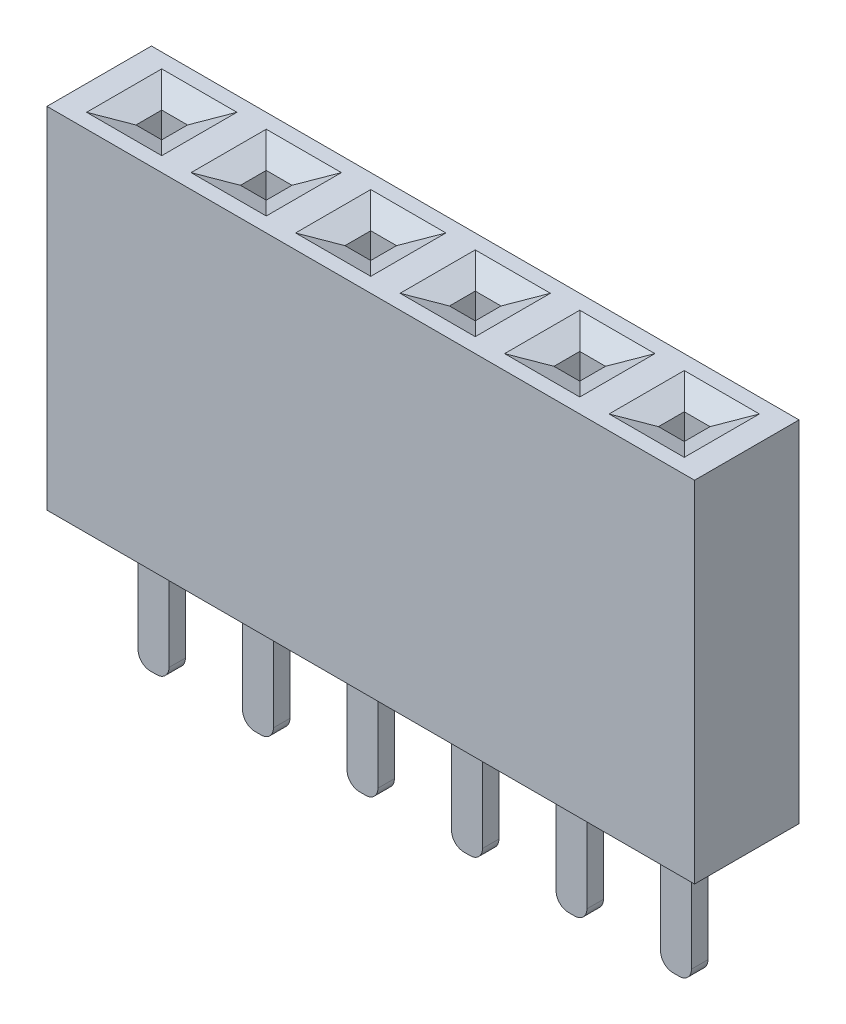
SolidWorks part; units mm, degrees
ref_plane "Plan de face" through (0, 0, 0) normal (0, 0, 1) x (1, 0, 0)
ref_plane "Plan de dessus" through (0, 0, 0) normal (0, 1, 0) x (1, 0, 0)
ref_plane "Plan de droite" through (0, 0, 0) normal (1, 0, 0) x (0, 0, -1)
sketch "Esquisse1" plane through (0, 0, 0) normal (0, 1, 0) x (1, 0, 0)
  line L1 (-7.87, 1.27) -> (7.87, 1.27)
  line L2 (-7.87, 1.27) -> (-7.87, -1.27)
  line L3 (-7.87, -1.27) -> (7.87, -1.27)
  line L4 (7.87, 1.27) -> (7.87, -1.27)
  line L5 (-7.87, 1.27) -> (7.87, -1.27) construction
  line L6 (-7.87, -1.27) -> (7.87, 1.27) construction
  point P0 (0, 0)
  dimension "D1" = 15.74
  dimension "D2" = 2.54
extrude "Boss.-Extru.1" add sketch "Esquisse1" along normal blind 8.5
sketch "Esquisse3" plane through (0, 8.5, 0) normal (0, 1, 0) x (1, 0, 0)
  line L0 (-8.36, 0.82) -> (8.2693, 0.82) construction
  line L1 (-8.36, -0.82) -> (8.2693, -0.82) construction
  line L2 (7.87, 1.27) -> (-7.87, 1.27) construction
  line L3 (-7.87, -1.27) -> (7.87, -1.27) construction
  line L4 (1.27, 1.6017) -> (1.27, -1.7521) construction
  line L5 (3.81, 1.6017) -> (3.81, -1.7521) construction
  line L6 (6.35, 1.6017) -> (6.35, -1.7521) construction
  line L7 (-1.27, 1.6017) -> (-1.27, -1.7521) construction
  line L8 (-3.81, 1.6017) -> (-3.81, -1.7521) construction
  line L9 (-6.35, 1.6017) -> (-6.35, -1.8488) construction
  line L10 (-8.36, 0) -> (8.2693, 0) construction
  line L12 (-2.09, 0.82) -> (-0.45, 0.82)
  line L13 (-2.09, 0.82) -> (-2.09, -0.82)
  line L14 (-2.09, -0.82) -> (-0.45, -0.82)
  line L15 (-0.45, 0.82) -> (-0.45, -0.82)
  line L16 (-2.09, 0.82) -> (-0.45, -0.82) construction
  line L17 (-2.09, -0.82) -> (-0.45, 0.82) construction
  line L18 (-4.63, 0.82) -> (-2.99, 0.82)
  line L19 (-4.63, 0.82) -> (-4.63, -0.82)
  line L20 (-4.63, -0.82) -> (-2.99, -0.82)
  line L21 (-2.99, 0.82) -> (-2.99, -0.82)
  line L22 (-4.63, 0.82) -> (-2.99, -0.82) construction
  line L23 (-4.63, -0.82) -> (-2.99, 0.82) construction
  line L24 (-7.17, 0.82) -> (-5.53, 0.82)
  line L25 (-7.17, 0.82) -> (-7.17, -0.82)
  line L26 (-7.17, -0.82) -> (-5.53, -0.82)
  line L27 (-5.53, 0.82) -> (-5.53, -0.82)
  line L28 (-7.17, 0.82) -> (-5.53, -0.82) construction
  line L29 (-7.17, -0.82) -> (-5.53, 0.82) construction
  line L30 (0.45, 0.82) -> (2.09, 0.82)
  line L31 (0.45, 0.82) -> (0.45, -0.82)
  line L32 (0.45, -0.82) -> (2.09, -0.82)
  line L33 (2.09, 0.82) -> (2.09, -0.82)
  line L34 (0.45, 0.82) -> (2.09, -0.82) construction
  line L35 (0.45, -0.82) -> (2.09, 0.82) construction
  line L36 (2.99, 0.82) -> (4.63, 0.82)
  line L37 (2.99, 0.82) -> (2.99, -0.82)
  line L38 (2.99, -0.82) -> (4.63, -0.82)
  line L39 (4.63, 0.82) -> (4.63, -0.82)
  line L40 (2.99, 0.82) -> (4.63, -0.82) construction
  line L41 (2.99, -0.82) -> (4.63, 0.82) construction
  line L42 (5.53, 0.82) -> (7.17, 0.82)
  line L43 (5.53, 0.82) -> (5.53, -0.82)
  line L44 (5.53, -0.82) -> (7.17, -0.82)
  line L45 (7.17, 0.82) -> (7.17, -0.82)
  line L46 (5.53, 0.82) -> (7.17, -0.82) construction
  line L47 (5.53, -0.82) -> (7.17, 0.82) construction
  line L48 (-6.6634, 0.3134) -> (-6.0366, 0.3134)
  line L49 (-6.6634, 0.3134) -> (-6.6634, -0.3134)
  line L50 (-6.6634, -0.3134) -> (-6.0366, -0.3134)
  line L51 (-6.0366, 0.3134) -> (-6.0366, -0.3134)
  line L52 (-6.6634, 0.3134) -> (-6.0366, -0.3134) construction
  line L53 (-6.6634, -0.3134) -> (-6.0366, 0.3134) construction
  line L54 (-4.1234, 0.3134) -> (-3.4966, 0.3134)
  line L55 (-4.1234, 0.3134) -> (-4.1234, -0.3134)
  line L56 (-4.1234, -0.3134) -> (-3.4966, -0.3134)
  line L57 (-3.4966, 0.3134) -> (-3.4966, -0.3134)
  line L58 (-4.1234, 0.3134) -> (-3.4966, -0.3134) construction
  line L59 (-4.1234, -0.3134) -> (-3.4966, 0.3134) construction
  line L60 (-1.5834, 0.3134) -> (-0.9566, 0.3134)
  line L61 (-1.5834, 0.3134) -> (-1.5834, -0.3134)
  line L62 (-1.5834, -0.3134) -> (-0.9566, -0.3134)
  line L63 (-0.9566, 0.3134) -> (-0.9566, -0.3134)
  line L64 (-1.5834, 0.3134) -> (-0.9566, -0.3134) construction
  line L65 (-1.5834, -0.3134) -> (-0.9566, 0.3134) construction
  line L66 (0.9566, 0.3134) -> (1.5834, 0.3134)
  line L67 (0.9566, 0.3134) -> (0.9566, -0.3134)
  line L68 (0.9566, -0.3134) -> (1.5834, -0.3134)
  line L69 (1.5834, 0.3134) -> (1.5834, -0.3134)
  line L70 (0.9566, 0.3134) -> (1.5834, -0.3134) construction
  line L71 (0.9566, -0.3134) -> (1.5834, 0.3134) construction
  line L72 (3.4966, 0.3134) -> (4.1234, 0.3134)
  line L73 (3.4966, 0.3134) -> (3.4966, -0.3134)
  line L74 (3.4966, -0.3134) -> (4.1234, -0.3134)
  line L75 (4.1234, 0.3134) -> (4.1234, -0.3134)
  line L76 (3.4966, 0.3134) -> (4.1234, -0.3134) construction
  line L77 (3.4966, -0.3134) -> (4.1234, 0.3134) construction
  line L78 (6.0366, 0.3134) -> (6.6634, 0.3134)
  line L79 (6.0366, 0.3134) -> (6.0366, -0.3134)
  line L80 (6.0366, -0.3134) -> (6.6634, -0.3134)
  line L81 (6.6634, 0.3134) -> (6.6634, -0.3134)
  line L82 (6.0366, 0.3134) -> (6.6634, -0.3134) construction
  line L83 (6.0366, -0.3134) -> (6.6634, 0.3134) construction
  point P23 (-1.27, 0)
  point P28 (-3.81, 0)
  point P33 (-6.35, 0)
  point P38 (1.27, 0)
  point P43 (3.81, 0)
  point P48 (6.35, 0)
  point P53 (-6.35, 0)
  point P58 (-3.81, 0)
  point P63 (-1.27, 0)
  point P68 (1.27, 0)
  point P73 (3.81, 0)
  point P78 (6.35, 0)
  dimension "D1" = 0.45
  dimension "D2" = 0.45
  dimension "D3" = 1.27
  dimension "D4" = 2.54
  dimension "D5" = 2.54
  dimension "D6" = 1.27
  dimension "D7" = 2.54
  dimension "D8" = 2.54
  dimension "D9" = 1.64
  dimension "D10" = 1.64
  dimension "D11" = 1.64
  dimension "D12" = 1.64
  dimension "D13" = 1.64
  dimension "D14" = 1.64
extrude "Enlèv. mat.-Extru.3" cut sketch "Esquisse3" against normal blind 8 contours L55 L56 L57 L54 | L51 L50 L49 L48 | L72 L75 L74 L73 | L67 L68 L69 L66 | L61 L62 L63 L60 | L79 L80 L81 L78
chamfer "Chanfrein3" distance 0.6 angle 24 24 edges at (6.35, 8.5, -0.3134) (6.6634, 8.5, 0) (6.35, 8.5, 0.3134) (6.0366, 8.5, 0) (3.81, 8.5, 0.3134) (4.1234, 8.5, 0) (3.81, 8.5, -0.3134) (3.4966, 8.5, 0) (1.27, 8.5, -0.3134) (1.5834, 8.5, 0) (1.27, 8.5, 0.3134) (0.9566, 8.5, 0) (-1.27, 8.5, 0.3134) (-0.9566, 8.5, 0) (-1.27, 8.5, -0.3134) (-1.5834, 8.5, 0) (-3.81, 8.5, 0.3134) (-3.4966, 8.5, 0) (-3.81, 8.5, -0.3134) (-4.1234, 8.5, 0) (-6.35, 8.5, 0.3134) (-6.0366, 8.5, 0) (-6.35, 8.5, -0.3134) (-6.6634, 8.5, 0)
sketch "Esquisse6" plane through (0, 0, 0) normal (0, -1, 0) x (1, 0, 0)
  line L0 (0, 1.6444) -> (0, -1.7496) construction
  line L1 (-1.27, 1.6444) -> (-1.27, -1.7496) construction
  line L2 (-3.81, 1.6444) -> (-3.81, -1.7496) construction
  line L3 (-6.35, 1.6444) -> (-6.35, -1.7496) construction
  line L4 (1.27, 1.6444) -> (1.27, -1.8565) construction
  line L5 (3.81, 1.6444) -> (3.81, -1.8565) construction
  line L6 (6.35, 1.6444) -> (6.35, -1.8565) construction
  line L7 (-8.2017, 0) -> (-7.8017, 0) construction
  line L9 (-6.725, 0.2) -> (-5.975, 0.2)
  line L10 (-6.725, 0.2) -> (-6.725, -0.2)
  line L11 (-6.725, -0.2) -> (-5.975, -0.2)
  line L12 (-5.975, 0.2) -> (-5.975, -0.2)
  line L13 (-6.725, 0.2) -> (-5.975, -0.2) construction
  line L14 (-6.725, -0.2) -> (-5.975, 0.2) construction
  line L15 (-4.185, 0.2) -> (-3.435, 0.2)
  line L16 (-4.185, 0.2) -> (-4.185, -0.2)
  line L17 (-4.185, -0.2) -> (-3.435, -0.2)
  line L18 (-3.435, 0.2) -> (-3.435, -0.2)
  line L19 (-4.185, 0.2) -> (-3.435, -0.2) construction
  line L20 (-4.185, -0.2) -> (-3.435, 0.2) construction
  line L21 (-1.645, 0.2) -> (-0.895, 0.2)
  line L22 (-1.645, 0.2) -> (-1.645, -0.2)
  line L23 (-1.645, -0.2) -> (-0.895, -0.2)
  line L24 (-0.895, 0.2) -> (-0.895, -0.2)
  line L25 (-1.645, 0.2) -> (-0.895, -0.2) construction
  line L26 (-1.645, -0.2) -> (-0.895, 0.2) construction
  line L27 (0.895, 0.2) -> (1.645, 0.2)
  line L28 (0.895, 0.2) -> (0.895, -0.2)
  line L29 (0.895, -0.2) -> (1.645, -0.2)
  line L30 (1.645, 0.2) -> (1.645, -0.2)
  line L31 (0.895, 0.2) -> (1.645, -0.2) construction
  line L32 (0.895, -0.2) -> (1.645, 0.2) construction
  line L33 (3.435, 0.2) -> (4.185, 0.2)
  line L34 (3.435, 0.2) -> (3.435, -0.2)
  line L35 (3.435, -0.2) -> (4.185, -0.2)
  line L36 (4.185, 0.2) -> (4.185, -0.2)
  line L37 (3.435, 0.2) -> (4.185, -0.2) construction
  line L38 (3.435, -0.2) -> (4.185, 0.2) construction
  line L39 (5.975, 0.2) -> (6.725, 0.2)
  line L40 (5.975, 0.2) -> (5.975, -0.2)
  line L41 (5.975, -0.2) -> (6.725, -0.2)
  line L42 (6.725, 0.2) -> (6.725, -0.2)
  line L43 (5.975, 0.2) -> (6.725, -0.2) construction
  line L44 (5.975, -0.2) -> (6.725, 0.2) construction
  point P17 (-6.35, 0)
  point P22 (-3.81, 0)
  point P27 (-1.27, 0)
  point P32 (1.27, 0)
  point P37 (3.81, 0)
  point P42 (6.35, 0)
  dimension "D1" = 1.27
  dimension "D2" = 1.27
  dimension "D3" = 2.54
  dimension "D4" = 2.54
  dimension "D5" = 2.54
  dimension "D6" = 2.54
  dimension "D7" = 0.75
  dimension "D8" = 0.4
  dimension "D9" = 0.75
  dimension "D10" = 0.4
  dimension "D11" = 0.75
  dimension "D12" = 0.4
  dimension "D13" = 0.75
  dimension "D14" = 0.4
  dimension "D15" = 0.75
  dimension "D16" = 0.4
  dimension "D17" = 0.75
  dimension "D18" = 0.4
extrude "Boss.-Extru.3" add sketch "Esquisse6" along normal blind 3.2
fillet "Congé1" radius 0.3 12 edges at (6.725, -3.2, 0) (5.975, -3.2, 0) (3.435, -3.2, 0) (4.185, -3.2, 0) (1.645, -3.2, 0) (0.895, -3.2, 0) (-0.895, -3.2, 0) (-1.645, -3.2, 0) (-3.435, -3.2, 0) (-4.185, -3.2, 0) (-5.975, -3.2, 0) (-6.725, -3.2, 0)
